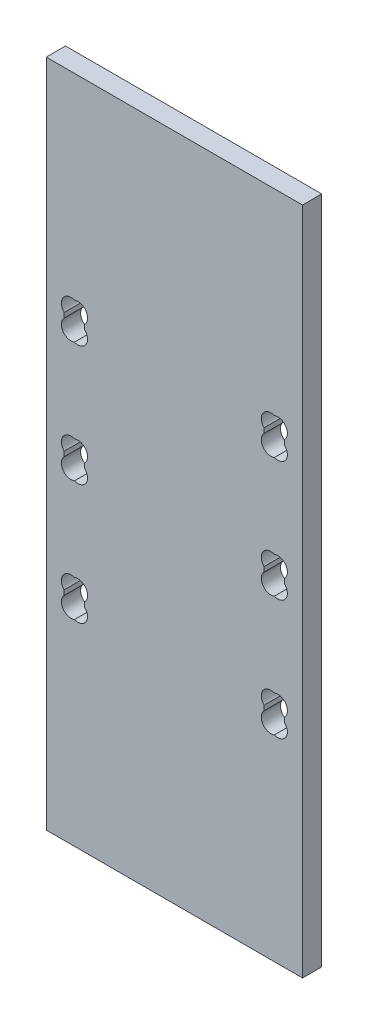
SolidWorks part; units mm, degrees
ref_plane "Alzado" through (0, 0, 0) normal (0, 0, 1) x (1, 0, 0)
ref_plane "Planta" through (0, 0, 0) normal (0, 1, 0) x (1, 0, 0)
ref_plane "Vista lateral" through (0, 0, 0) normal (1, 0, 0) x (0, 0, -1)
sketch "Croquis2" plane through (0, 0, 0) normal (0, 0, 1) x (1, 0, 0)
  line L1 (-20, -52.25) -> (20, -52.25)
  line L2 (-20, -52.25) -> (-20, 52.25)
  line L3 (-20, 52.25) -> (20, 52.25)
  line L4 (20, -52.25) -> (20, 52.25)
  line L5 (-20, -52.25) -> (20, 52.25) construction
  line L6 (-20, 52.25) -> (20, -52.25) construction
  point P0 (0, 0)
  dimension "D1" = 40
  dimension "D2" = 104.5
extrude "Saliente-Extruir1" add sketch "Croquis2" along normal blind 3
sketch "Croquis3" plane through (0, 0, 3) normal (0, 0, 1) x (1, 0, 0)
  line L0 (14, 21.25) -> (14, 52.25) construction
  line L1 (14, 21.25) -> (17.2, 21.25)
  line L2 (14, 21.25) -> (14, 16.25)
  line L3 (14, 16.25) -> (17.2, 16.25)
  line L4 (17.2, 21.25) -> (17.2, 16.25)
  line L5 (14, 2.5) -> (17.2, 2.5)
  line L6 (14, 2.5) -> (14, -2.5)
  line L7 (14, -2.5) -> (17.2, -2.5)
  line L8 (17.2, 2.5) -> (17.2, -2.5)
  line L9 (14, -16.25) -> (17.2, -16.25)
  line L10 (14, -16.25) -> (14, -21.25)
  line L11 (14, -21.25) -> (17.2, -21.25)
  line L12 (17.2, -16.25) -> (17.2, -21.25)
  line L13 (20, 52.25) -> (-20, 52.25) construction
  line L14 (14, 16.25) -> (14, 2.5) construction
  line L15 (14, -2.5) -> (14, -16.25) construction
  line L16 (14, -21.25) -> (14, -52.25) construction
  line L17 (-20, -52.25) -> (20, -52.25) construction
  line L18 (20, -52.25) -> (20, 52.25) construction
  line L19 (0, 0) -> (0, 52.25) construction
  line L20 (-17.2, 21.25) -> (-17.2, 16.25)
  line L21 (-14, 16.25) -> (-17.2, 16.25)
  line L22 (-14, 21.25) -> (-14, 16.25)
  line L23 (-14, 21.25) -> (-17.2, 21.25)
  line L24 (-17.2, 2.5) -> (-17.2, -2.5)
  line L25 (-14, -2.5) -> (-17.2, -2.5)
  line L26 (-14, 2.5) -> (-14, -2.5)
  line L27 (-14, 2.5) -> (-17.2, 2.5)
  line L28 (-17.2, -16.25) -> (-17.2, -21.25)
  line L29 (-14, -21.25) -> (-17.2, -21.25)
  line L30 (-14, -16.25) -> (-14, -21.25)
  line L31 (-14, -16.25) -> (-17.2, -16.25)
  dimension "D1" = 3.2
  dimension "D2" = 5
  dimension "D3" = 13.75
  dimension "D4" = 6
extrude "Cortar-Extruir1" cut sketch "Croquis3" against normal through all
sketch "Croquis4" plane through (0, 0, 3) normal (0, 0, 1) x (1, 0, 0)
  line L0 (14, 21.25) -> (15.5, 19.75) construction
  line L1 (17.2, 21.25) -> (14, 21.25) construction
  line L2 (14, 21.25) -> (14, 16.25) construction
  line L3 (15.6, 16.25) -> (15.6, 19.2747) construction
  line L5 (14, 16.25) -> (17.2, 16.25) construction
  line L6 (17.2, 18.75) -> (13.3268, 18.75) construction
  line L7 (17.2, 16.25) -> (17.2, 21.25) construction
  circle A0 centre (15.5, 19.75) radius 1.5 construction
  circle A1 centre (15.0607, 20.1893) radius 1.5
  circle A2 centre (16.1393, 20.1893) radius 1.5
  circle A3 centre (16.1393, 17.3107) radius 1.5
  circle A4 centre (15.0607, 17.3107) radius 1.5
  dimension "D1" = 3
extrude "Cortar-Extruir3" cut sketch "Croquis4" against normal blind 3 contours A2 | A1 | A4 | A3
sketch "Croquis5" plane through (0, 0, 3) normal (0, 0, 1) x (1, 0, 0)
  line L0 (14, 19.1287) -> (14, 18.3713) construction
  line L1 (17.2, 18.3713) -> (17.2, 19.1287) construction
  line L2 (14, 19.1287) -> (14, 18.3713) construction
  line L3 (17.2, 18.3713) -> (17.2, 19.1287) construction
  line L4 (-15.6, 16.25) -> (21.6689, 16.25) construction
  line L6 (15.6, 9.375) -> (-20, 9.375) construction
  line L7 (14, -2.5) -> (17.2, -2.5) construction
  line L8 (15.6, -2.5) -> (15.6, -16.25) construction
  line L9 (17.2, -16.25) -> (14, -16.25) construction
  line L10 (-20, 52.25) -> (-20, -52.25) construction
  line L11 (0, 52.25) -> (0, 0) construction
  line L12 (15.6, -9.375) -> (-20, -9.375) construction
  line L13 (20, 52.25) -> (-20, 52.25) construction
  line L14 (-17.2, 16.25) -> (-14, 16.25) construction
  line L15 (15.6, 2.5) -> (15.6, 16.25) construction
  line L16 (17.2, 2.5) -> (14, 2.5) construction
  line L17 (17.2, 0.3787) -> (17.2, -0.3787)
  line L18 (14, -0.3787) -> (14, 0.3787)
  line L19 (14, -18.3713) -> (14, -19.1287)
  line L20 (17.2, -19.1287) -> (17.2, -18.3713)
  line L21 (-17.2, -19.1287) -> (-17.2, -18.3713)
  line L22 (-14, -18.3713) -> (-14, -19.1287)
  line L23 (-14, -0.3787) -> (-14, 0.3787)
  line L24 (-17.2, 0.3787) -> (-17.2, -0.3787)
  line L25 (-17.2, 18.3713) -> (-17.2, 19.1287)
  line L26 (-14, 19.1287) -> (-14, 18.3713)
  arc A0 (17.2, 19.1287) -> (15.6, 21.589) centre (16.1393, 20.1893) ccw construction
  arc A1 (15.6, 21.589) -> (14, 19.1287) centre (15.0607, 20.1893) ccw construction
  arc A2 (14, 18.3713) -> (15.6, 15.911) centre (15.0607, 17.3107) ccw construction
  arc A3 (15.6, 15.911) -> (17.2, 18.3713) centre (16.1393, 17.3107) ccw construction
  arc A4 (17.2, 19.1287) -> (15.6, 21.589) centre (16.1393, 20.1893) ccw construction
  arc A5 (15.6, 21.589) -> (14, 19.1287) centre (15.0607, 20.1893) ccw construction
  arc A6 (14, 18.3713) -> (15.6, 15.911) centre (15.0607, 17.3107) ccw construction
  arc A7 (15.6, 15.911) -> (17.2, 18.3713) centre (16.1393, 17.3107) ccw construction
  arc A8 (15.6, 2.839) -> (17.2, 0.3787) centre (16.1393, 1.4393) cw
  arc A9 (14, 0.3787) -> (15.6, 2.839) centre (15.0607, 1.4393) cw
  arc A10 (15.6, -2.839) -> (14, -0.3787) centre (15.0607, -1.4393) cw
  arc A11 (17.2, -0.3787) -> (15.6, -2.839) centre (16.1393, -1.4393) cw
  arc A12 (17.2, -18.3713) -> (15.6, -15.911) centre (16.1393, -17.3107) ccw
  arc A13 (15.6, -15.911) -> (14, -18.3713) centre (15.0607, -17.3107) ccw
  arc A14 (14, -19.1287) -> (15.6, -21.589) centre (15.0607, -20.1893) ccw
  arc A15 (15.6, -21.589) -> (17.2, -19.1287) centre (16.1393, -20.1893) ccw
  arc A16 (-15.6, -21.589) -> (-17.2, -19.1287) centre (-16.1393, -20.1893) cw
  arc A17 (-14, -19.1287) -> (-15.6, -21.589) centre (-15.0607, -20.1893) cw
  arc A18 (-15.6, -15.911) -> (-14, -18.3713) centre (-15.0607, -17.3107) cw
  arc A19 (-17.2, -18.3713) -> (-15.6, -15.911) centre (-16.1393, -17.3107) cw
  arc A20 (-17.2, -0.3787) -> (-15.6, -2.839) centre (-16.1393, -1.4393) ccw
  arc A21 (-15.6, -2.839) -> (-14, -0.3787) centre (-15.0607, -1.4393) ccw
  arc A22 (-14, 0.3787) -> (-15.6, 2.839) centre (-15.0607, 1.4393) ccw
  arc A23 (-15.6, 2.839) -> (-17.2, 0.3787) centre (-16.1393, 1.4393) ccw
  arc A24 (-15.6, 15.911) -> (-17.2, 18.3713) centre (-16.1393, 17.3107) cw
  arc A25 (-14, 18.3713) -> (-15.6, 15.911) centre (-15.0607, 17.3107) cw
  arc A26 (-15.6, 21.589) -> (-14, 19.1287) centre (-15.0607, 20.1893) cw
  arc A27 (-17.2, 19.1287) -> (-15.6, 21.589) centre (-16.1393, 20.1893) cw
extrude "Cortar-Extruir4" cut sketch "Croquis5" against normal through all
